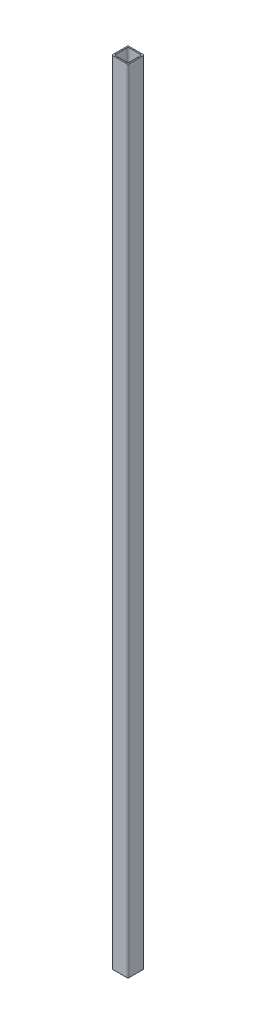
SolidWorks part; units mm, degrees
material "Hexcel AS4C (3000 Filaments)"
ref_plane "Front Plane" through (0, 0, 0) normal (0, 0, 1) x (1, 0, 0)
ref_plane "Top Plane" through (0, 0, 0) normal (0, 1, 0) x (1, 0, 0)
ref_plane "Right Plane" through (0, 0, 0) normal (1, 0, 0) x (0, 0, -1)
sketch "Sketch1" plane through (0, 0, 0) normal (0, 1, 0) x (1, 0, 0)
  line L1 (-9, -10) -> (9, -10)
  line L2 (-10, -9) -> (-10, 9)
  line L3 (-9, 10) -> (9, 10)
  line L4 (10, -9) -> (10, 9)
  line L5 (-10, -10) -> (10, 10) construction
  line L6 (-10, 10) -> (10, -10) construction
  line L7 (-7.5, -8.5) -> (7.5, -8.5)
  line L8 (-8.5, -7.5) -> (-8.5, 7.5)
  line L9 (-7.5, 8.5) -> (7.5, 8.5)
  line L10 (8.5, -7.5) -> (8.5, 7.5)
  line L11 (-8.5, -8.5) -> (8.5, 8.5) construction
  line L12 (-8.5, 8.5) -> (8.5, -8.5) construction
  arc A0 (-9, -10) -> (-10, -9) centre (-9, -9) cw
  arc A1 (9, 10) -> (10, 9) centre (9, 9) cw
  arc A2 (9, -10) -> (10, -9) centre (9, -9) ccw
  arc A3 (-10, 9) -> (-9, 10) centre (-9, 9) cw
  arc A4 (-7.5, -8.5) -> (-8.5, -7.5) centre (-7.5, -7.5) cw
  arc A5 (7.5, -8.5) -> (8.5, -7.5) centre (7.5, -7.5) ccw
  arc A6 (7.5, 8.5) -> (8.5, 7.5) centre (7.5, 7.5) cw
  arc A7 (-8.5, 7.5) -> (-7.5, 8.5) centre (-7.5, 7.5) cw
  point P0 (0, 0)
  point P18 (0, 0)
  dimension "D3" = 1
  dimension "D6" = 1
  dimension "D7" = 1
  dimension "D8" = 1
  dimension "D9" = 1
  dimension "D1" = 20
  dimension "D2" = 20
  dimension "D4" = 17
  dimension "D5" = 17
extrude "Boss-Extrude1" add sketch "Sketch1" along normal blind 1200
sketch "Sketch2" plane through (0, 0, 0) normal (0, -1, 0) x (1, 0, 0)
  line L1 (-46.6317, 52.4419) -> (55.2633, 52.4419)
  line L2 (-46.6317, 52.4419) -> (-46.6317, -85.6856)
  line L3 (-46.6317, -85.6856) -> (55.2633, -85.6856)
  line L4 (55.2633, 52.4419) -> (55.2633, -85.6856)
extrude "Cut-Extrude1" cut sketch "Sketch2" against normal blind 220
